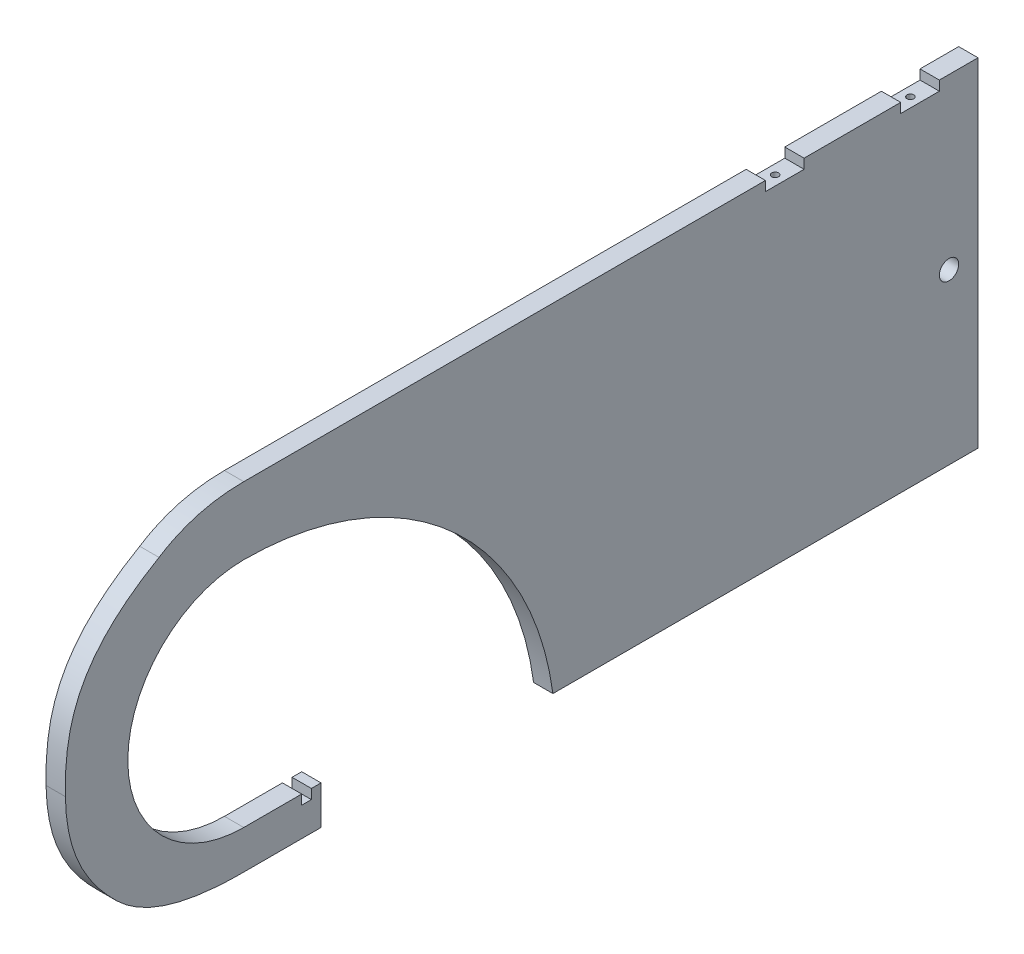
SolidWorks part; units mm, degrees
material "6061-T6 (SS)"
ref_plane "Front Plane" through (0, 0, 0) normal (0, 0, 1) x (1, 0, 0)
ref_plane "Top Plane" through (0, 0, 0) normal (0, 1, 0) x (1, 0, 0)
ref_plane "Right Plane" through (0, 0, 0) normal (1, 0, 0) x (0, 0, -1)
sketch "Sketch1" plane through (0, 0, 0) normal (1, 0, 0) x (0, 0, -1)
  line L0 (0, 38.1) -> (0, -38.1) construction
  line L13 (25.4, -50.8) -> (25.4, -38.1)
  line L14 (25.4, -38.1) -> (22.225, -38.1)
  line L15 (22.225, -38.1) -> (22.225, -41.275)
  line L16 (22.225, -41.275) -> (19.05, -41.275)
  line L17 (19.05, -41.275) -> (19.05, -38.1)
  line L18 (19.05, -38.1) -> (0, -38.1)
  line L19 (0, 60.325) -> (171.45, 60.325)
  line L22 (241.3, -50.8) -> (101.6, -50.8)
  line L23 (0, -50.8) -> (25.4, -50.8)
  line L38 (171.45, -50.8) -> (171.45, 60.325) construction
  line L39 (241.3, -50.8) -> (241.3, 60.325)
  line L42 (184.15, 57.15) -> (184.15, 60.325)
  line L44 (228.6, 57.15) -> (228.6, 60.325)
  line L46 (171.45, 60.325) -> (171.45, 57.15)
  line L47 (184.15, 60.325) -> (215.9, 60.325)
  line L48 (215.9, 60.325) -> (215.9, 57.15)
  line L49 (228.6, 60.325) -> (241.3, 60.325)
  line L50 (184.15, 57.15) -> (171.45, 57.15)
  line L51 (215.9, 57.15) -> (228.6, 57.15)
  line L52 (241.3, 4.7625) -> (231.775, 4.7625) construction
  arc A0 (0, 38.1) -> (0, -38.1) centre (0, 0) ccw
  arc A4 (0, 38.1) -> (101.6, -50.8) centre (0, -64.4071) cw
  circle A6 centre (231.775, 4.7625) radius 3.175
  spline S0 degree 2 poles (0, -50.8) (-28.6718, -50.9225) (-41.7522, -38.1) knots 0 0 0 0.219145 0.219145 0.219145
  spline S1 degree 3 poles (-58.6251, 0) (-58.9953, 19.7851) (-54.9318, 37.0439) (-27.8409, 52.6855) knots 0.494452 0.494452 0.494452 0.494452 0.821555 0.821555 0.821555 0.821555
  spline S2 degree 2 poles (-27.8409, 52.6855) (-15.9703, 60.3278) (0, 60.325) knots 0.821555 0.821555 0.821555 1 1 1
  spline S3 degree 3 poles (-41.7522, -38.1) (-52.7073, -27.3609) (-58.3234, -16.1263) (-58.6251, 0) knots 0.219145 0.219145 0.219145 0.219145 0.494452 0.494452 0.494452 0.494452
  point P4 (0, 0)
  dimension "D1" = 76.2
  dimension "D2" = 22.225
  dimension "D5" = 139.7
  dimension "D9" = 19.05
  dimension "D8" = 9.525
  dimension "D7" = 6.35
  dimension "D3" = 12.7
  dimension "D4" = 3.175
  dimension "D6" = 76.2
  dimension "D13" = 3.175
  dimension "D14" = 12.7
  dimension "D15" = 31.75
  dimension "D20" = 12.7
  dimension "D21" = 12.7
sketch "Sketch2" plane through (0, 0, 0) normal (1, 0, 0) x (0, 0, -1)
  line L0 (103.1875, -39.6875) -> (20.6375, -39.6875) construction
  line L1 (0, 38.1) -> (0, -38.1) construction
  line L2 (103.1875, -39.6875) -> (51.1724, 24.4135) construction
  line L3 (-35.3701, -14.1622) -> (-18.0046, 33.5775) construction
  line L8 (22.225, -41.275) -> (19.05, -41.275) construction
  line L9 (19.05, -41.275) -> (19.05, -38.1) construction
  line L10 (-35.3701, -14.1622) -> (12.3697, -31.5277) construction
  line L11 (12.3697, -31.5277) -> (29.7351, 16.212) construction
  line L12 (-18.0046, 33.5775) -> (29.7351, 16.212) construction
  line L13 (-35.3701, -14.1622) -> (29.7351, 16.212) construction
  line L14 (12.3697, -31.5277) -> (-18.0046, 33.5775) construction
  arc A0 (0, -38.1) -> (0, 38.1) centre (0, 0) ccw construction
  arc A1 (51.1724, 24.4135) -> (20.6375, -39.6875) centre (103.1875, -39.6875) ccw construction
  arc A3 (0, 38.1) -> (0, -38.1) centre (0, 0) ccw construction
  arc A4 (101.6, -50.8) -> (0, 38.1) centre (0, -64.4071) ccw construction
  point P33 (-2.8175, 1.0249)
  point P44 (-2.8175, 1.0249)
  dimension "D4" = 50.8
  dimension "D1" = 82.55
  dimension "D2" = 1.5875
  dimension "D3" = 1.5875
extrude "Boss-Extrude2" add sketch "Sketch1" along normal mid plane 6.35
hole_wizard "#4-40 Tapped Hole1" positions "Sketch3" profile "Sketch4" tap size "#4-40" standard "ANSI Inch"
sketch "Sketch3" plane through (0, 57.15, 0) normal (0, 1, 0) x (1, 0, 0)
  line L0 (0, 215.9) -> (0, 228.6) construction
  line L1 (3.175, 171.45) -> (-3.175, 171.45) construction
  point P0 (0, 177.8)
  point P2 (0, 222.25)
  point P7 (0, 177.8)
  dimension "D1" = 6.35
sketch "Sketch4" plane through (0, 57.15, -177.8) normal (1, 0, 0) x (0, 0, 1)
  line L0 (0, 0) -> (0, 8.2992)
  line L1 (0, 8.2992) -> (1.1303, 7.62)
  line L2 (1.1303, 7.62) -> (1.1303, 0)
  line L5 (1.1303, 0) -> (0, 0)
  line L10 (0, 8.2992) -> (-1.1303, 7.62) construction
  line L11 (0, -6.35) -> (0, 107.95) construction
  dimension "Tap Drill Dia." = 2.2606
  dimension "Tap Drill Depth" = 7.62
  dimension "Drill Angle" = 118
cosmetic thread "Hole Thread1" parameters "D1"=5.588, "D2"=2.8448
cosmetic thread "Hole Thread2" parameters "D1"=5.588, "D2"=2.8448
cosmetic thread "Hole Thread3" parameters "D1"=5.588, "D2"=2.8448
equation "\"Thick\"= \"in\""
